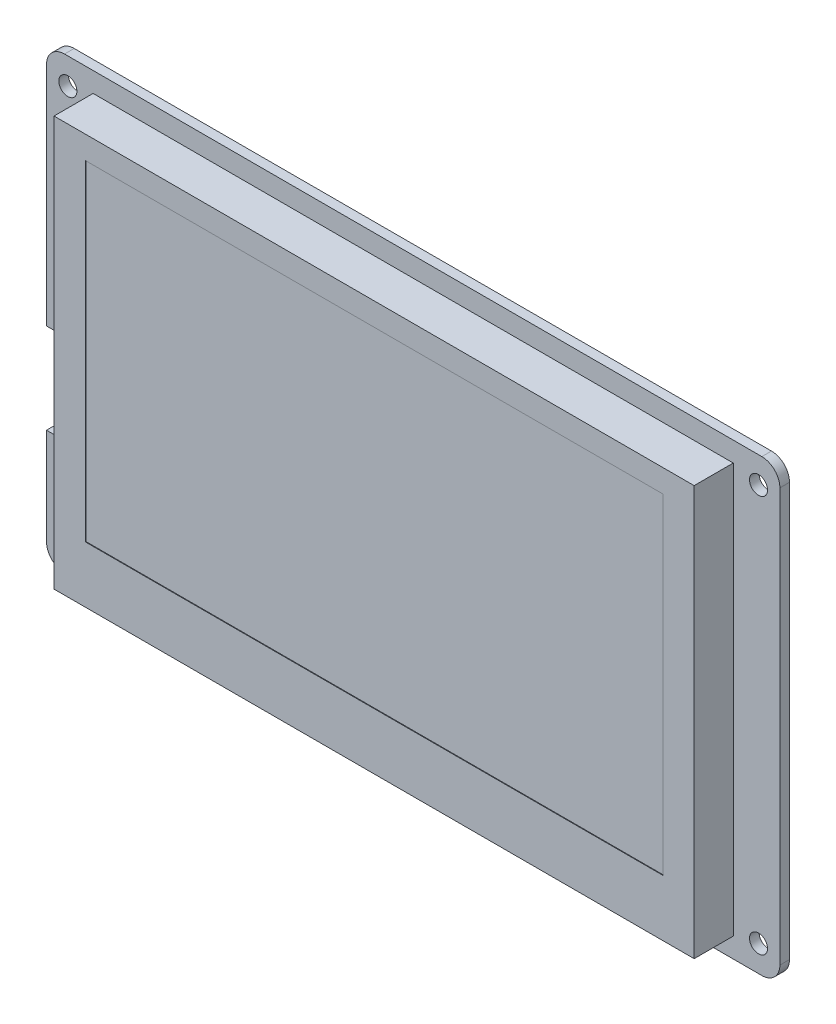
SolidWorks part; units mm, degrees
ref_plane "前视基准面" through (0, 0, 0) normal (0, 0, 1) x (1, 0, 0)
ref_plane "上视基准面" through (0, 0, 0) normal (0, 1, 0) x (1, 0, 0)
ref_plane "右视基准面" through (0, 0, 0) normal (1, 0, 0) x (0, 0, -1)
sketch "草图1" plane through (0, 0, 0) normal (0, 0, 1) x (1, 0, 0)
  line L1 (-60.95, -37.35) -> (60.95, -37.35)
  line L2 (-60.95, -37.35) -> (-60.95, 37.35)
  line L3 (-60.95, 37.35) -> (60.95, 37.35)
  line L4 (60.95, -37.35) -> (60.95, 37.35)
  line L5 (-60.95, -37.35) -> (60.95, 37.35) construction
  line L6 (-60.95, 37.35) -> (60.95, -37.35) construction
  point P0 (0, 0)
  dimension "D1" = 121.9
  dimension "D2" = 74.7
extrude "凸台-拉伸1" add sketch "草图1" along normal blind 1.6
sketch "草图2" plane through (0, 0, 1.6) normal (0, 0, 1) x (1, 0, 0)
  line L0 (0, 37.35) -> (0, -37.35) construction
  line L1 (60.95, 37.35) -> (-60.95, 37.35) construction
  line L2 (-60.95, -37.35) -> (60.95, -37.35) construction
  line L4 (-57.4, -33) -> (57.4, -33) construction
  line L5 (-57.4, -33) -> (-57.4, 33) construction
  line L6 (-57.4, 33) -> (57.4, 33) construction
  line L7 (57.4, -33) -> (57.4, 33) construction
  line L8 (-57.4, -33) -> (57.4, 33) construction
  line L9 (-57.4, 33) -> (57.4, -33) construction
  circle A0 centre (-57.4, 33) radius 1.5
  circle A1 centre (-57.4, -33) radius 1.5
  circle A2 centre (57.4, -33) radius 1.5
  circle A3 centre (57.4, 33) radius 1.5
  point P6 (0, 0)
  dimension "D4" = 3
  dimension "D1" = 66
  dimension "D2" = 114.8
  dimension "D3" = 4.35
extrude "切除-拉伸1" cut sketch "草图2" against normal blind 1.6
fillet "圆角1" radius 3 4 edges at (-60.95, 37.35, 0.8) (-60.95, -37.35, 0.8) (60.95, -37.35, 0.8) (60.95, 37.35, 0.8)
sketch "草图3" plane through (0, 0, 1.6) normal (0, 0, 1) x (1, 0, 0)
  line L1 (-53.2, -34.05) -> (53.2, -34.05)
  line L2 (-53.2, -34.05) -> (-53.2, 34.05)
  line L3 (-53.2, 34.05) -> (53.2, 34.05)
  line L4 (53.2, -34.05) -> (53.2, 34.05)
  line L5 (-53.2, -34.05) -> (53.2, 34.05) construction
  line L6 (-53.2, 34.05) -> (53.2, -34.05) construction
  point P0 (0, 0)
  dimension "D1" = 68.1
  dimension "D2" = 106.4
extrude "凸台-拉伸2" add sketch "草图3" along normal blind 6.5
sketch "草图4" plane through (0, 0, 8.1) normal (0, 0, 1) x (1, 0, 0)
  line L0 (-44.0338, 2.8) -> (37.5568, 2.8) construction
  line L3 (0, 34.05) -> (0, -34.05) construction
  line L4 (53.2, 34.05) -> (-53.2, 34.05) construction
  line L5 (-53.2, -34.05) -> (53.2, -34.05) construction
  line L7 (-48, -24.65) -> (48, -24.65)
  line L8 (-48, -24.65) -> (-48, 30.25)
  line L9 (-48, 30.25) -> (48, 30.25)
  line L10 (48, -24.65) -> (48, 30.25)
  line L11 (-48, -24.65) -> (48, 30.25) construction
  line L12 (-48, 30.25) -> (48, -24.65) construction
  circle A1 centre (-57.4, 33) radius 1.5 construction
  point P10 (0, 2.8)
  dimension "D1" = 30.2
  dimension "D2" = 54.9
  dimension "D3" = 96
extrude "切除-拉伸2" cut sketch "草图4" against normal blind 0.1
sketch "草图6" plane through (0, 0, 0) normal (0, 0, -1) x (-1, 0, 0)
  line L0 (60.95, 34.35) -> (60.95, -34.35) construction
  line L1 (56.75, -18.3) -> (70.3236, -18.3)
  line L2 (56.75, -18.3) -> (56.75, -3.3)
  line L3 (56.75, -3.3) -> (70.3236, -3.3)
  line L4 (70.3236, -18.3) -> (70.3236, -3.3)
  line L5 (56.75, -18.3) -> (70.3236, -3.3) construction
  line L6 (56.75, -3.3) -> (70.3236, -18.3) construction
  circle A0 centre (57.4, -33) radius 1.5 construction
  point P0 (63.5368, -10.8)
  dimension "D1" = 22.2
  dimension "D2" = 15
  dimension "D3" = 4.2
extrude "切除-拉伸3" cut sketch "草图6" against normal through all
sketch "草图7" plane through (0, 0, 0) normal (0, 0, -1) x (-1, 0, 0)
  line L0 (60.95, 34.35) -> (60.95, -3.3) construction
  line L1 (-57.95, 37.35) -> (57.95, 37.35) construction
  circle A0 centre (40.95, 25.35) radius 5
  dimension "D1" = 20
  dimension "D3" = 10
  dimension "D2" = 12
extrude "凸台-拉伸3" add sketch "草图7" along normal blind 5.7
sketch "草图8" [suppressed] plane through (0, 0, 8.1) normal (0, 0, 1) x (1, 0, 0)
  line L0 (-48, 2.8) -> (48, 2.8) construction
  line L3 (-48, 30.25) -> (-48, -24.65) construction
  line L4 (48, -24.65) -> (48, 30.25) construction
  line L7 (53.2, 34.05) -> (-53.2, 34.05) construction
